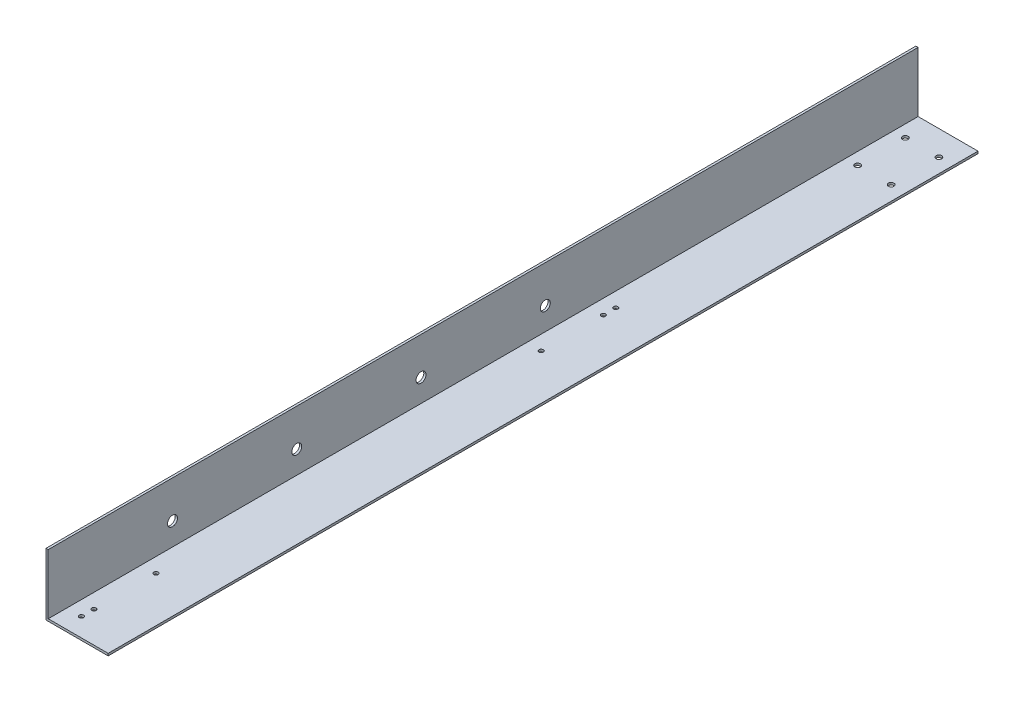
SolidWorks part; units mm, degrees
ref_plane "前基準面" through (0, 0, 0) normal (0, 0, 1) x (1, 0, 0)
ref_plane "上基準面" through (0, 0, 0) normal (0, 1, 0) x (1, 0, 0)
ref_plane "右基準面" through (0, 0, 0) normal (1, 0, 0) x (0, 0, -1)
sketch "草圖1" plane through (0, 0, 0) normal (0, 0, 1) x (1, 0, 0)
  line L0 (0, 50) -> (0, 0)
  line L1 (0, 0) -> (50, 0)
  line L2 (0, 50) -> (1.8, 50)
  line L3 (1.8, 50) -> (1.8, 1.8)
  line L4 (1.8, 1.8) -> (50, 1.8)
  line L5 (50, 1.8) -> (50, 0)
  dimension "D1" = 50
  dimension "D2" = 50
  dimension "D3" = 1.8
  dimension "D4" = 1.8
  dimension "D5" = 48.2
  dimension "D6" = 48.2
extrude "填料-伸長1" add sketch "草圖1" along normal blind 700 contours L0 L1 L5 L4 L3 L2
ref_plane "平面1" through (0, 0, 0) normal (0, -1, 0) x (-1, 0, 0)
ref_plane "平面2" through (0, 0, 0) normal (0, -1, 0) x (-1, 0, 0)
sketch "草圖2" plane through (0, 0, 0) normal (0, -1, 0) x (-1, 0, 0)
  line L0 (0, 0) -> (-50, 0) construction
  line L1 (-50, -700) -> (-50, 0) construction
  line L2 (-11.5, -20) -> (-11.5, -58.34) construction
  line L6 (-38.5, -700) -> (-38.5, -20) construction
  line L7 (0, -700) -> (-50, -700) construction
  circle A0 centre (-38.5, -20) radius 2.25
  circle A1 centre (-38.5, -58.34) radius 2.25
  circle A2 centre (-11.5, -20) radius 2.25
  circle A3 centre (-11.5, -58.34) radius 2.25
  dimension "D1" = 11.5
  dimension "D2" = 20
  dimension "D3" = 38.34
  dimension "D4" = 4.5
  dimension "D5" = 4.5
  dimension "D6" = 4.5
  dimension "D7" = 4.5
  dimension "D8" = 27
  dimension "D9" = 20
  dimension "D10" = 38.34
extrude "除料-伸長1" cut sketch "草圖2" against normal blind 10
sketch "草圖3" plane through (0, 0, 0) normal (-1, 0, 0) x (0, 0, 1)
  line L0 (700, 20) -> (11.1392, 20) construction
  line L1 (700, 50) -> (700, 0) construction
  line L2 (700, 0) -> (0, 0) construction
  circle A0 centre (600, 20) radius 4
  circle A1 centre (500, 20) radius 4
  circle A2 centre (400, 20) radius 4
  circle A3 centre (300, 20) radius 4
  dimension "D2" = 100
  dimension "D1" = 20
  dimension "D3" = 200
  dimension "D4" = 300
  dimension "D5" = 400
extrude "除料-伸長2" cut sketch "草圖3" against normal through all
hole_wizard "Ø3.5 (3.5) 直徑孔1" positions "草圖10" profile "草圖9" hole size "Ø3.5" standard "JIS"
sketch "草圖10" plane through (0, 0, 0) normal (0, -1, 0) x (-1, 0, 0)
  line L0 (-13.5, -700) -> (-13.5, 0) construction
  line L1 (0, -700) -> (-50, -700) construction
  line L2 (0, 0) -> (-50, 0) construction
  line L5 (0, -700) -> (0, 0) construction
  point P16 (-13.5, -685)
  point P18 (-13.5, -675)
  point P20 (-13.5, -625)
  point P23 (-13.5, -255)
  point P26 (-13.5, -265)
  point P28 (-13.5, -315)
  dimension "D1" = 13.5
  dimension "D2" = 15
  dimension "D3" = 10
  dimension "D4" = 50
  dimension "D5" = 445
  dimension "D6" = 10
  dimension "D7" = 50
sketch "草圖9" plane through (13.5, 0, 685) normal (1, 0, 0) x (0, 0, -1)
  line L0 (0, 0) -> (0, 3.0515)
  line L1 (0, 3.0515) -> (1.75, 2)
  line L2 (1.75, 2) -> (1.75, 0)
  line L5 (1.75, 0) -> (0, 0)
  line L10 (0, 3.0515) -> (-1.75, 2) construction
  line L11 (0, -6.35) -> (0, 107.95) construction
  dimension "鑽孔直徑" = 3.5
  dimension "鑽孔深度" = 2
  dimension "導頭角度" = 118
